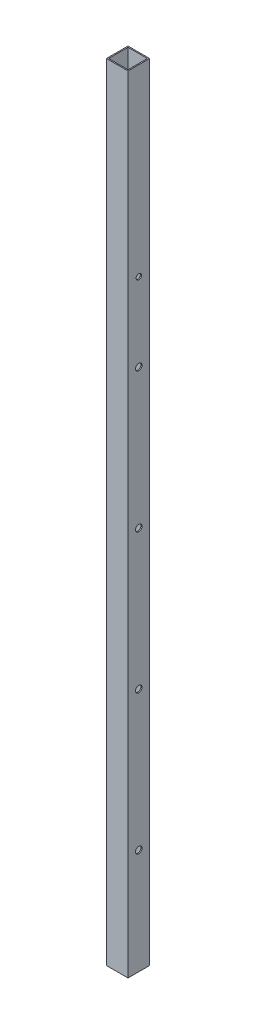
SolidWorks part; units mm, degrees
ref_plane "Alzado" through (0, 0, 0) normal (0, 0, 1) x (1, 0, 0)
ref_plane "Planta" through (0, 0, 0) normal (0, 1, 0) x (1, 0, 0)
ref_plane "Vista lateral" through (0, 0, 0) normal (1, 0, 0) x (0, 0, -1)
sketch "Croquis1" plane through (0, 0, 0) normal (0, 1, 0) x (1, 0, 0)
  line L0 (-28.575, 28.575) -> (28.575, 28.575)
  line L1 (-31.75, -31.75) -> (31.75, -31.75)
  line L2 (-31.75, -31.75) -> (-31.75, 31.75)
  line L3 (-31.75, 31.75) -> (31.75, 31.75)
  line L4 (31.75, -31.75) -> (31.75, 31.75)
  line L5 (-31.75, -31.75) -> (31.75, 31.75) construction
  line L6 (-31.75, 31.75) -> (31.75, -31.75) construction
  line L7 (28.575, -28.575) -> (28.575, 28.575)
  line L8 (-28.575, -28.575) -> (28.575, -28.575)
  line L9 (-28.575, -28.575) -> (-28.575, 28.575)
  point P0 (0, 0)
  dimension "D1" = 63.5
  dimension "D2" = 63.5
  dimension "D3" = 3.175
extrude "Saliente-Extruir1" add sketch "Croquis1" along normal blind 2400
sketch "Croquis2" plane through (31.75, 0, 0) normal (1, 0, 0) x (0, 0, -1)
  line L0 (0, 0) -> (0, 400) construction
  circle A0 centre (0, 400) radius 9.525
  dimension "D2" = 19.05
  dimension "D1" = 400
extrude "Cortar-Extruir1" cut sketch "Croquis2" against normal blind 450
pattern_linear "MatrizL1" count 4 spacing 410 along (0, 1, 0) of "Cortar-Extruir1"
sketch "Croquis3" plane through (-31.75, 0, 0) normal (-1, 0, 0) x (0, 0, 1)
  line L0 (31.75, 2400) -> (31.75, 0) construction
  line L1 (-31.75, 0) -> (31.75, 0)
  line L2 (-31.75, 0) -> (-31.75, 90)
  line L3 (-31.75, 90) -> (31.75, 90)
  line L4 (31.75, 0) -> (31.75, 90)
  dimension "D1" = 90
extrude "Cortar-Extruir2" cut sketch "Croquis3" against normal blind 200
sketch "Croquis4" plane through (-31.75, 0, 0) normal (-1, 0, 0) x (0, 0, 1)
  line L0 (0, 2400) -> (0, 1860) construction
  line L1 (-31.75, 2400) -> (31.75, 2400) construction
  circle A0 centre (0, 1860) radius 7.9375
  dimension "D2" = 15.875
  dimension "D1" = 540
extrude "Cortar-Extruir3" cut sketch "Croquis4" against normal up to surface (63.5 mm away) up to face at (31.75, 810, -9.525)
